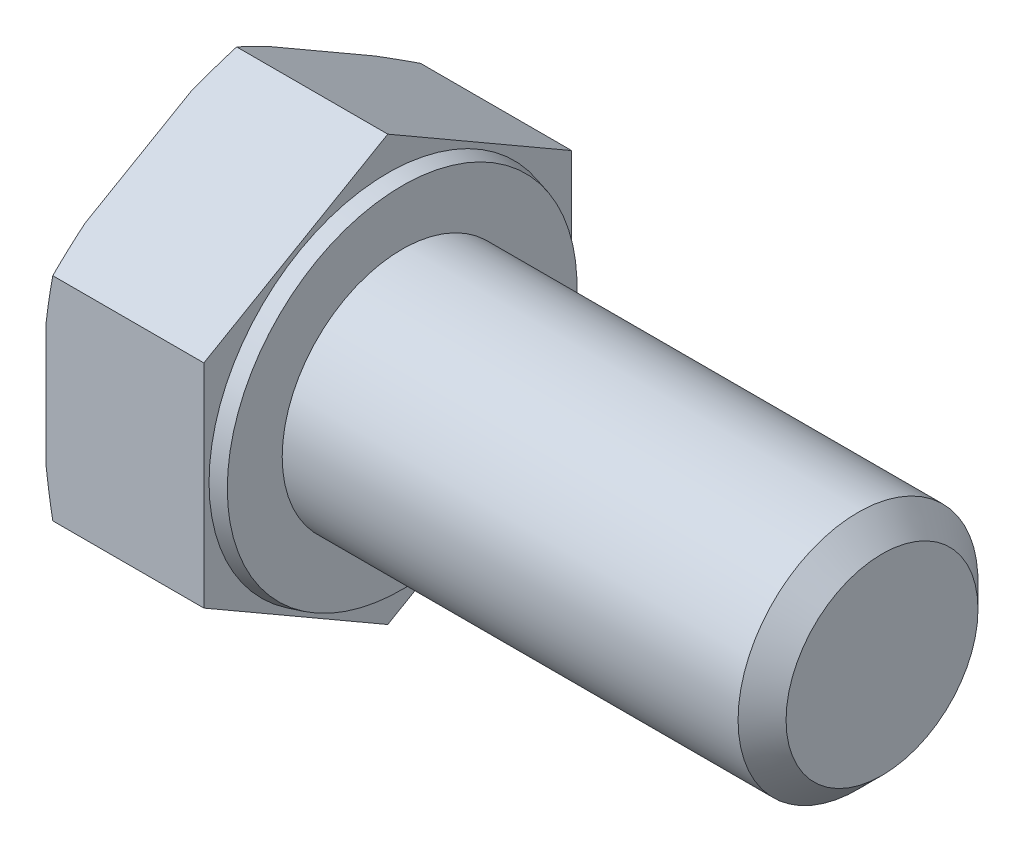
SolidWorks part; units mm, degrees
material "AISI 1020"
ref_plane "Спереди" through (0, 0, 0) normal (0, 0, 1) x (1, 0, 0)
ref_plane "Сверху" through (0, 0, 0) normal (0, 1, 0) x (1, 0, 0)
ref_plane "Справа" through (0, 0, 0) normal (1, 0, 0) x (0, 0, -1)
sketch "Эскиз1" plane through (0, 0, 0) normal (0, 0, 1) x (1, 0, 0)
  line L0 (-1000, 0) -> (49000, 0) construction
  line L1 (-6.58, 0) -> (-6.58, 8.85)
  line L2 (-6.58, 8.85) -> (0, 8.85)
  line L3 (0, 8.85) -> (0, 7.449)
  line L4 (0.6, 5) -> (20.6, 5)
  line L5 (20.6, 5) -> (20.6, 0)
  line L6 (-6.58, 0) -> (20.6, 0)
  line L7 (0, 7.449) -> (0.6, 7.2882)
  line L8 (0.6, 7.2882) -> (0.6, 5)
  line L9 (0.5, 0) -> (0.5, 7.315) construction
  dimension "_d" = 10
  dimension "D1" = 20
  dimension "D5" = 17.7
  dimension "D2" = 0.6
  dimension "D3" = 6.58
  dimension "D4" = 0.1
  dimension "D6" = 14.63
  dimension "D7" = 75
revolve "Повернуть1" add sketch "Эскиз1" angle 360 about L0
sketch "Эскиз2" plane through (-6.58, 0, 0) normal (-1, 0, 0) x (0, 0, 1)
  line L1 (0, -8.85) -> (7.6643, -4.425)
  line L2 (7.6643, -4.425) -> (7.6643, 4.425)
  line L3 (7.6643, 4.425) -> (0, 8.85)
  line L4 (0, 8.85) -> (-7.6643, 4.425)
  line L5 (-7.6643, 4.425) -> (-7.6643, -4.425)
  line L6 (-7.6643, -4.425) -> (0, -8.85)
  circle A0 centre (0, 0) radius 7.6643 construction
  circle A1 centre (0, 0) radius 8.85 construction
extrude "Вырез-Вытянуть1" cut sketch "Эскиз2" against normal through all flip side to cut
sketch "Эскиз4" plane through (0, 0, 0) normal (0, 0, 1) x (1, 0, 0)
  line L0 (-1000, 0) -> (49000, 0) construction
  line L1 (-6.58, 8.075) -> (-6.2979, 8.85)
  line L2 (-6.2979, 8.85) -> (-6.58, 8.85)
  line L3 (-6.58, 8.85) -> (-6.58, 8.075)
  line L4 (-6.58, 4.425) -> (-6.58, 8.85) construction
  line L6 (0, 8.85) -> (-6.58, 8.85) construction
  dimension "D1" = 20
  dimension "D2" = 16.15
revolve "Вырез-Повернуть1" cut sketch "Эскиз4" angle 360 about L0
chamfer "Фаска1" distance 1 angle 45 1 edges at (20.6, 0, 5)
equation "\"l\"= 20'длина болта"
equation "\"_d\"= 10'диаметр болта"
equation "\"b\"= 20'длина резьбы"
equation "\"k\"= 6.58'толщина шляпки"
equation "\"e\"= 17.7'диаметр головки описанный"
equation "\"S\"= 17'размер под ключ"
equation "\"_d@Эскиз1\"=\"_d\""
equation "\"dw\"= 14.63"
equation "\"da\"= 9.78"
equation "\"с\"= 0.6"
equation "\"D1@Эскиз1\"=\"l\""
equation "\"D5@Эскиз1\"=\"e\""
equation "\"D2@Эскиз1\"=\"с\""
equation "\"D3@Эскиз1\"=\"k\""
equation "\"D2@Эскиз4\"=\"S\"*0.95"
equation "\"D1@Фаска1\"=\"_d\"/10"
equation "\"D6@Эскиз1\"=\"dw\""
